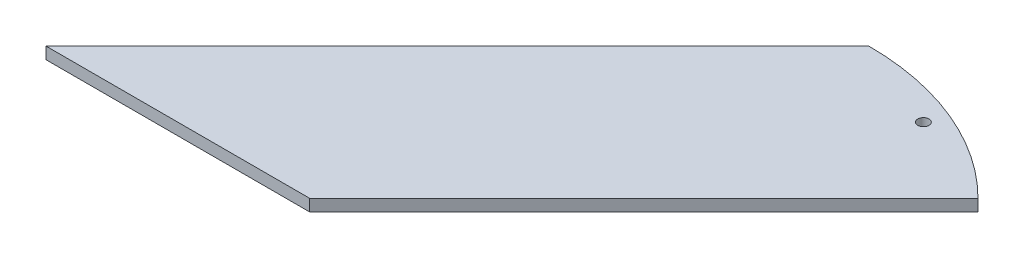
SolidWorks part; units mm, degrees
ref_plane "Front Plane" through (0, 0, 0) normal (0, 0, 1) x (1, 0, 0)
ref_plane "Top Plane" through (0, 0, 0) normal (0, 1, 0) x (1, 0, 0)
ref_plane "Right Plane" through (0, 0, 0) normal (1, 0, 0) x (0, 0, -1)
sketch "Sketch1" plane through (0, 0, 0) normal (0, 1, 0) x (1, 0, 0)
  line L7 (-135.3553, -75) -> (-64.6447, -75)
  line L9 (-64.6447, -75) -> (25, 14.6447)
  line L13 (-135.3553, -75) -> (-25, 35.3553)
  circle A0 centre (0, 25) radius 1.5
  circle A1 centre (0, 25) radius 1.5
  arc A2 (-25, 35.3553) -> (25, 14.6447) centre (-25, -35.3553) cw
  point P0 (0, 0)
  point P1 (0, 0)
  point P2 (-17.6777, 7.3223)
  point P19 (0, 25)
  dimension "D1" = 3
  dimension "D4" = 2
extrude "Boss-Extrude1" add sketch "Sketch1" along normal blind 3.175 contours A2 L13 L7 L9 A0
